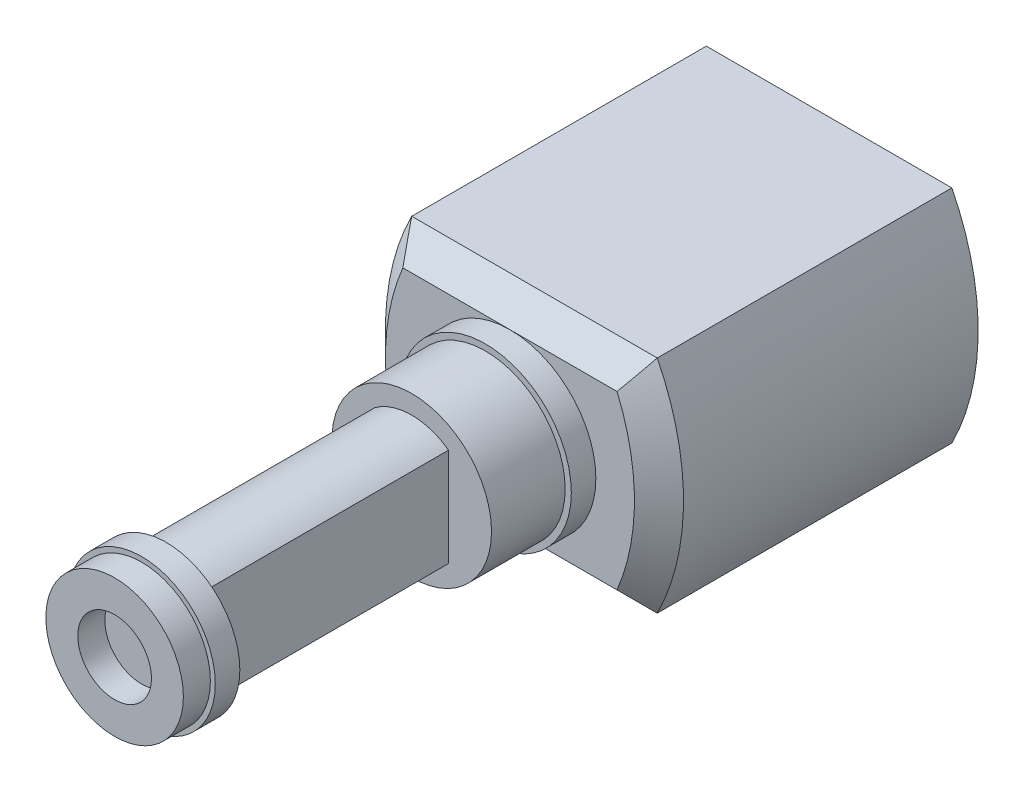
SolidWorks part; units mm, degrees
ref_plane "Front Plane" through (0, 0, 0) normal (0, 0, 1) x (1, 0, 0)
ref_plane "Top Plane" through (0, 0, 0) normal (0, 1, 0) x (1, 0, 0)
ref_plane "Right Plane" through (0, 0, 0) normal (1, 0, 0) x (0, 0, -1)
sketch "Sketch1" plane through (0, 0, 0) normal (0, 0, 1) x (1, 0, 0)
  line L0 (0, -81.8182) -> (0, 81.8182) construction
  line L1 (-104.0727, 0) -> (104.0727, 0) construction
  line L2 (-50, 45) -> (50, 45)
  line L3 (-50, -45) -> (50, -45)
  arc A0 (-50, 45) -> (-50, -45) centre (39.3029, 0) ccw
  arc A1 (50, 45) -> (50, -45) centre (-39.3029, 0) cw
  point P4 (0, 0)
  point P8 (0, 0)
  dimension "D2" = 100
  dimension "D1" = 100
  dimension "45" = 45
extrude "Boss-Extrude1" add sketch "Sketch1" along normal blind 120
sketch "Sketch2" plane through (0, 0, 120) normal (0, 0, 1) x (1, 0, 0)
  line L2 (-50, -45) -> (50, -45)
  line L3 (50, 45) -> (-50, 45)
  line L4 (-50, -45) -> (50, -45)
  line L5 (50, 45) -> (-50, 45)
  arc A2 (-50, 45) -> (-50, -45) centre (39.3029, 0) ccw
  arc A3 (50, -45) -> (50, 45) centre (-39.3029, 0) ccw
  arc A4 (-50, 45) -> (-50, -45) centre (39.3029, 0) ccw
  arc A5 (50, -45) -> (50, 45) centre (-39.3029, 0) ccw
  dimension "D1" = 0
extrude "Boss-Extrude2" add sketch "Sketch2" along normal blind 10 draft 45
sketch "Sketch3" plane through (0, 0, 130) normal (0, 0, 1) x (1, 0, 0)
  circle A0 centre (0, 0) radius 35
  dimension "D1" = 70
extrude "Boss-Extrude3" add sketch "Sketch3" along normal blind 10
sketch "Sketch4" plane through (0, 0, 140) normal (0, 0, 1) x (1, 0, 0)
  circle A0 centre (0, 0) radius 32.5
  dimension "D1" = 65
extrude "Boss-Extrude4" add sketch "Sketch4" along normal blind 30
sketch "Sketch5" plane through (0, 0, 170) normal (0, 0, 1) x (1, 0, 0)
  line L0 (0, 0) -> (0, -24.7414) construction
  line L1 (0, -24.7414) -> (0, 27.5114) construction
  line L4 (0, 0) -> (-26.5041, 0) construction
  line L5 (-15, 20) -> (-15, -20)
  line L6 (15, 20) -> (15, -20)
  arc A0 (-15, 20) -> (15, 20) centre (0, -0.6763) cw
  arc A1 (-15, -20) -> (15, -20) centre (0, 0.6763) ccw
  dimension "D3" = 25.5442
  dimension "D1" = 40
  dimension "D2" = 15
extrude "Boss-Extrude5" add sketch "Sketch5" along normal blind 100
sketch "Sketch6" plane through (0, 0, 270) normal (0, 0, 1) x (1, 0, 0)
  circle A0 centre (0, 0) radius 30
  dimension "D1" = 60
extrude "Boss-Extrude6" add sketch "Sketch6" along normal blind 10
sketch "Sketch7" plane through (0, 0, 280) normal (0, 0, 1) x (1, 0, 0)
  circle A0 centre (0, 0) radius 28
  circle A1 centre (0, 0) radius 30 construction
  dimension "D1" = 2
extrude "Boss-Extrude7" add sketch "Sketch7" along normal blind 11
ref_plane "Plane1" through (-50, 0, 0) normal (-1, 0, 0) x (0, 0, 1)
sketch "Sketch8" plane through (-50, 0, 0) normal (-1, 0, 0) x (0, 0, 1)
  line L0 (120, -45) -> (0, -45) construction
  circle A0 centre (60, -45) radius 40
  dimension "D1" = 80
extrude "Boss-Extrude8" add sketch "Sketch8" along normal mid plane 22
sketch "Sketch9" plane through (-39, 0, 0) normal (1, 0, 0) x (0, 0, -1)
  line L0 (-60, -45) -> (-60, -97.0353) construction
  line L1 (-20, -45) -> (-100, -45) construction
  line L2 (-85, -45) -> (-35, -45)
  line L3 (-120, -45) -> (0, -45) construction
  line L4 (-35, -45) -> (-35, -72)
  line L5 (-85, -45) -> (-85, -72)
  arc A0 (-85, -72) -> (-35, -72) centre (-60, -9.3852) ccw
  point P9 (-63.5515, -45)
  dimension "D3" = 67.4212
  dimension "D1" = 25
  dimension "D2" = 27
extrude "Boss-Extrude9" add sketch "Sketch9" along normal blind 55
sketch "Sketch10" plane through (0, 0, 291) normal (0, 0, 1) x (1, 0, 0)
  circle A0 centre (0, 0) radius 15
  dimension "D1" = 30
extrude "Cut-Extrude1" cut sketch "Sketch10" against normal blind 11
sketch "Sketch11" plane through (-61, 0, 0) normal (-1, 0, 0) x (0, 0, 1)
  circle A0 centre (60, -45) radius 15
  dimension "D1" = 30
extrude "Cut-Extrude2" cut sketch "Sketch11" against normal blind 20
